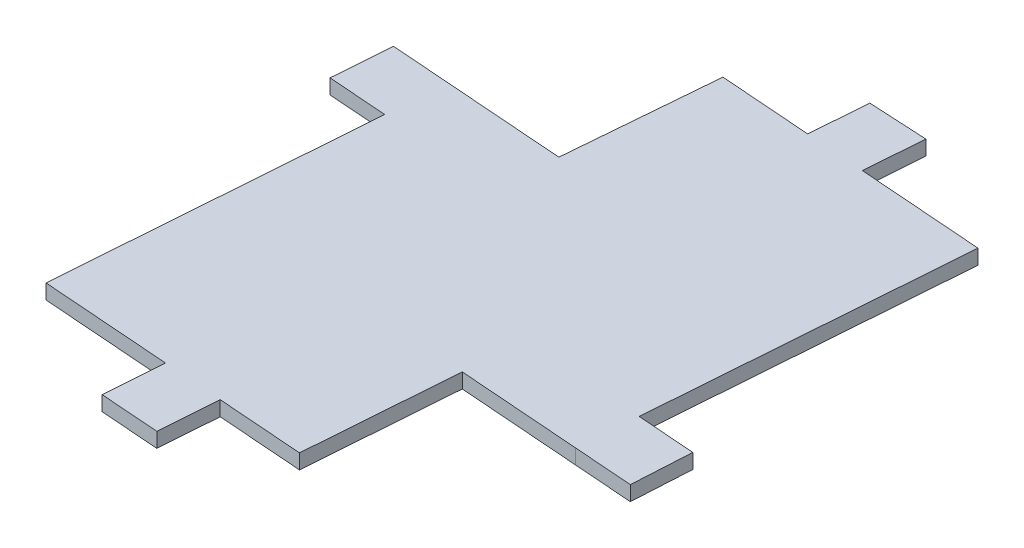
SolidWorks part; units mm, degrees
material "ABS"
ref_plane "Front Plane" through (0, 0, 0) normal (0, 0, 1) x (1, 0, 0)
ref_plane "Top Plane" through (0, 0, 0) normal (0, 1, 0) x (1, 0, 0)
ref_plane "Right Plane" through (0, 0, 0) normal (1, 0, 0) x (0, 0, -1)
sketch "Sketch1" plane through (0, 0, 0) normal (0, 1, 0) x (1, 0, 0)
  line L0 (4.5685, 43.5426) -> (3.9859, 35.7342)
  line L1 (3.9859, 35.7342) -> (-8.3864, 36.6574)
  line L2 (-8.3864, 36.6574) -> (-10.1055, 16.2162)
  line L3 (-26.2607, 17.4215) -> (-34.2385, 18.0168)
  line L4 (-34.2385, 18.0168) -> (-34.8337, 10.039)
  line L5 (-34.8337, 10.039) -> (-26.8559, 9.4437)
  line L6 (-26.8559, 9.4437) -> (-30.0322, -33.1255)
  line L7 (-30.0322, -33.1255) -> (-12.5806, -34.4276)
  line L8 (-12.5806, -34.4276) -> (-13.1759, -42.4054)
  line L9 (-13.1759, -42.4054) -> (-5.1981, -43.0007)
  line L10 (-5.1981, -43.0007) -> (-4.6028, -35.0229)
  line L11 (-4.6028, -35.0229) -> (6.965, -35.886)
  line L12 (6.965, -35.886) -> (8.4919, -15.4226)
  line L13 (8.4919, -15.4226) -> (25.0508, -16.666)
  line L14 (25.0508, -16.666) -> (33.0232, -17.2608)
  line L15 (-10.1055, 16.2162) -> (-26.2607, 17.4215)
  line L16 (33.0232, -17.2608) -> (33.4789, -9.2731)
  line L17 (33.4789, -9.2731) -> (25.6461, -8.6881)
  line L18 (25.6461, -8.6881) -> (28.8424, 33.8795)
  line L19 (28.8424, 33.8795) -> (11.9637, 35.1389)
  line L20 (11.9637, 35.1389) -> (12.559, 43.1168)
  line L21 (12.559, 43.1168) -> (4.5685, 43.5426)
extrude "Boss-Extrude1" add sketch "Sketch1" along normal blind 2
